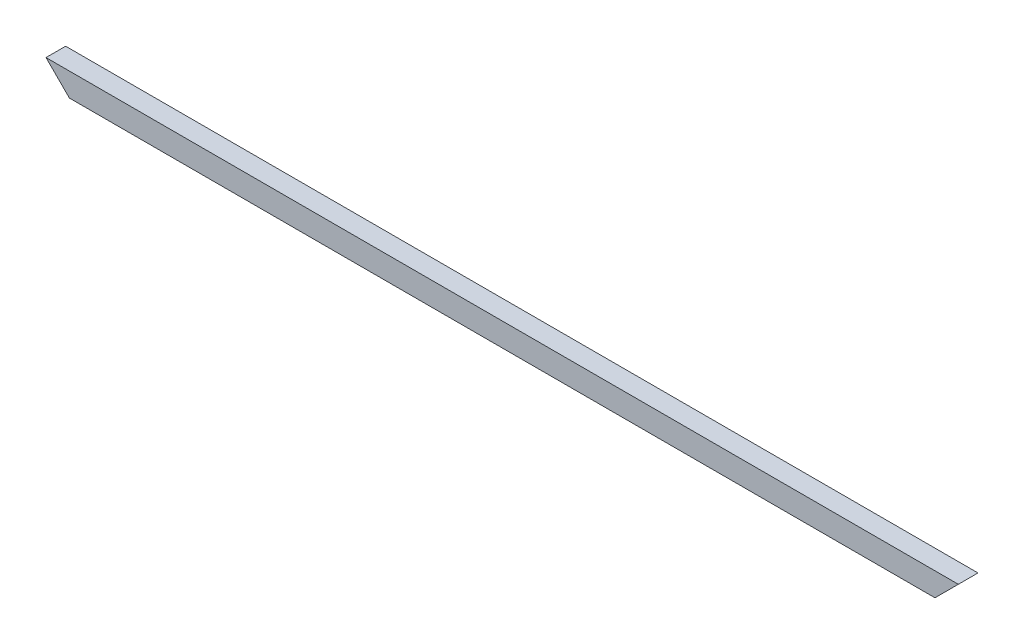
SolidWorks part; units mm, degrees
material "6063-O"
ref_plane "Front Plane" through (0, 0, 0) normal (0, 0, 1) x (1, 0, 0)
ref_plane "Top Plane" through (0, 0, 0) normal (0, 1, 0) x (1, 0, 0)
ref_plane "Right Plane" through (0, 0, 0) normal (1, 0, 0) x (0, 0, -1)
sketch "Sketch1" plane through (0, 0, 0) normal (1, 0, 0) x (0, 0, -1)
  line L0 (-6.35, 0) -> (6.35, 0)
  line L1 (6.35, 0) -> (6.35, -17.4)
  line L3 (-6.35, -17.4) -> (-6.35, 0)
  line L4 (-8, -17.4) -> (-8, 1.65)
  line L5 (-8, 1.65) -> (8, 1.65)
  line L6 (8, 1.65) -> (8, -17.4)
  line L7 (-6.35, -17.4) -> (-8, -17.4)
  line L8 (6.35, -17.4) -> (8, -17.4)
  point P4 (0, 0)
  dimension "D1" = 12.7
  dimension "D2" = 19.05
  dimension "D3" = 16
extrude "Boss-Extrude1" add sketch "Sketch1" along normal mid plane 742.95
sketch "Sketch4" plane through (0, 1.65, 0) normal (0, 1, 0) x (1, 0, 0)
  line L0 (371.475, 8) -> (355.475, -8)
  line L1 (371.475, -8) -> (-371.475, -8) construction
  line L2 (355.475, -8) -> (371.475, -8)
  line L3 (371.475, -8) -> (-371.475, -8) construction
  line L4 (371.475, 8) -> (-371.475, 8) construction
  line L6 (371.475, -8) -> (371.475, 8)
  line L7 (371.475, 8) -> (-371.475, 8) construction
  line L8 (371.475, 8) -> (371.475, -8) construction
  line L9 (371.475, 8) -> (-371.475, 8) construction
  dimension "D1" = 45
extrude "Cut-Right-Top" [suppressed] cut sketch "Sketch4" against normal through all and the other way through all
sketch "Sketch7" plane through (0, 0, -8) normal (0, 0, -1) x (-1, 0, 0)
  line L0 (-371.475, 1.65) -> (-352.425, -17.4)
  line L1 (-371.475, -17.4) -> (371.475, -17.4) construction
  line L2 (-371.475, -17.4) -> (-371.475, 1.65) construction
  line L3 (-371.475, 1.65) -> (-371.475, -17.4)
  line L4 (-371.475, -17.4) -> (-352.425, -17.4)
  dimension "D1" = 45
extrude "Cut-Right-Side-Top" cut sketch "Sketch7" against normal through all and the other way through all
sketch "Sketch8" [suppressed] plane through (0, 0, -8) normal (0, 0, -1) x (-1, 0, 0)
  line L0 (-278.765, -17.4) -> (-259.715, 1.65)
  line L1 (-278.765, 1.65) -> (278.765, 1.65) construction
  line L2 (-259.715, 1.65) -> (-278.765, 1.65)
  line L3 (-278.765, 1.65) -> (-278.765, -17.4)
  line L4 (-259.715, -17.4) -> (278.765, -17.4) construction
  line L5 (-278.765, 1.65) -> (278.765, 1.65) construction
  line L7 (-278.765, 1.65) -> (278.765, 1.65) construction
  line L8 (-297.815, -17.4) -> (-278.765, 1.65) construction
  dimension "D1" = 45
extrude "Cut-Right-Side-Bottom" [suppressed] cut sketch "Sketch8" against normal through all and the other way through all
sketch "Sketch5" plane through (0, 0, -8) normal (0, 0, -1) x (-1, 0, 0)
  line L0 (371.475, 1.65) -> (352.425, -17.4)
  line L1 (-352.425, -17.4) -> (371.475, -17.4) construction
  line L2 (352.425, -17.4) -> (371.475, -17.4)
  line L3 (371.475, -17.4) -> (371.475, 1.65)
  line L4 (-371.475, 1.65) -> (371.475, 1.65) construction
  dimension "D1" = 45
extrude "Cut-Left-Side-Top" cut sketch "Sketch5" against normal through all and the other way through all
sketch "Sketch9" [suppressed] plane through (0, 0, -8) normal (0, 0, -1) x (-1, 0, 0)
  line L0 (278.765, -17.4) -> (259.715, 1.65)
  line L1 (-278.765, 1.65) -> (278.765, 1.65) construction
  line L2 (278.765, -17.4) -> (278.765, 1.65)
  line L3 (278.765, 1.65) -> (259.715, 1.65)
  dimension "D1" = 45
extrude "Cut-Left-Side-Bottom" [suppressed] cut sketch "Sketch9" against normal through all and the other way through all
sketch "Sketch6" [suppressed] plane through (0, 1.65, 0) normal (0, 1, 0) x (1, 0, 0)
  line L0 (-278.765, 8) -> (-262.765, -8)
  line L1 (278.765, -8) -> (-278.765, -8) construction
  line L4 (-278.765, 8) -> (-278.765, -8)
  line L6 (278.765, -8) -> (-278.765, -8) construction
  line L7 (278.765, 8) -> (-278.765, 8) construction
  line L8 (-278.765, -8) -> (-262.765, -8)
  line L9 (278.765, 8) -> (-278.765, 8) construction
  dimension "D1" = 45
extrude "Cut-Left-Top" [suppressed] cut sketch "Sketch6" against normal through all and the other way through all
